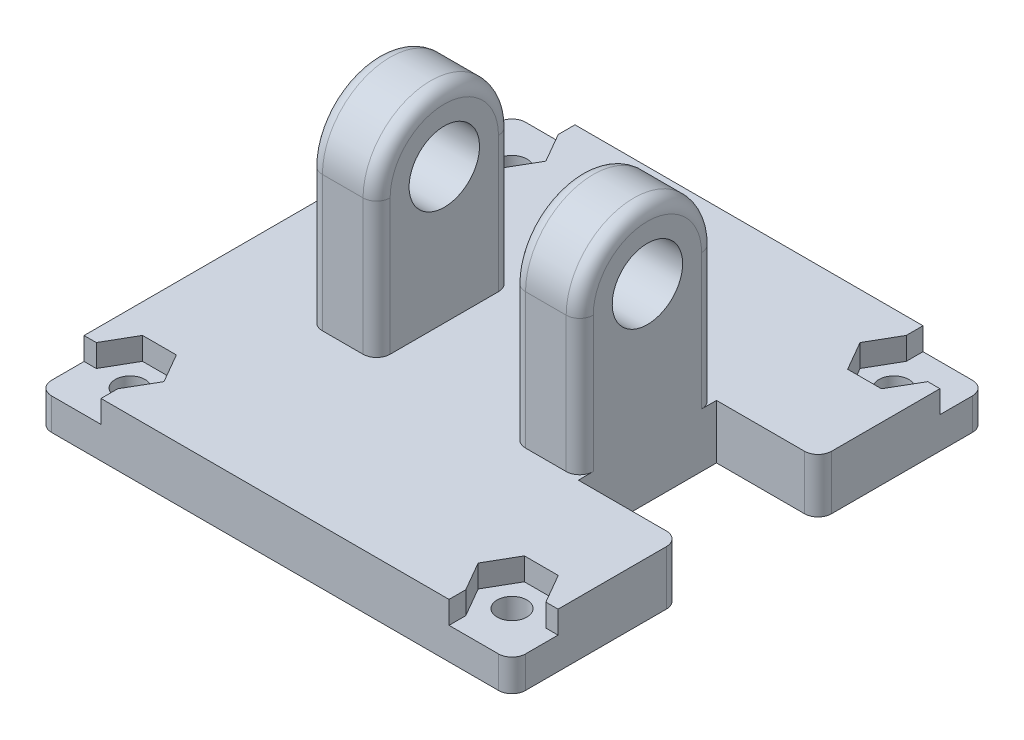
SolidWorks part; units mm, degrees
ref_plane "Plan de face" through (0, 0, 0) normal (0, 0, 1) x (1, 0, 0)
ref_plane "Plan de dessus" through (0, 0, 0) normal (0, 1, 0) x (1, 0, 0)
ref_plane "Plan de droite" through (0, 0, 0) normal (1, 0, 0) x (0, 0, -1)
sketch "Esquisse2" plane through (0, 0, 0) normal (1, 0, 0) x (0, 0, -1)
  line L0 (5, 0) -> (5, -10)
  line L2 (-5, 0) -> (-5, -10)
  line L3 (-5, -10) -> (5, -10)
  circle A0 centre (0, 0) radius 2.6
  arc A2 (5, 0) -> (-5, 0) centre (0, 0) ccw
  dimension "D1" = 5.2
  dimension "D2" = 10
  dimension "D3" = 5
  dimension "D4" = 5
extrude "Boss.-Extru.1" add sketch "Esquisse2" along normal mid plane 20
sketch "Esquisse4" plane through (0, -10, 0) normal (0, -1, 0) x (1, 0, 0)
  line L1 (-17.5, -17.5) -> (17.5, -17.5)
  line L2 (-17.5, -17.5) -> (-17.5, 17.5)
  line L3 (-17.5, 17.5) -> (17.5, 17.5)
  line L4 (17.5, -17.5) -> (17.5, 17.5)
  dimension "D1" = 35
  dimension "D2" = 35
  dimension "D3" = 17.5
  dimension "D4" = 17.5
extrude "Boss.-Extru.2" add sketch "Esquisse4" along normal blind 4
sketch "Esquisse5" plane through (0, -10, 0) normal (0, 1, 0) x (1, 0, 0)
  circle A0 centre (14.1, -14.1) radius 1.1
  circle A1 centre (14.1, 14.1) radius 1.1
  circle A2 centre (-14.1, 14.1) radius 1.1
  circle A3 centre (-14.1, -14.1) radius 1.1
  point P15 (0, 0)
  dimension "D1" = 2.2
  dimension "D2" = 28.2
  dimension "D3" = 28.2
  dimension "D4" = 14.1
  dimension "D5" = 14.1
extrude "Enlèv. mat.-Extru.1" cut sketch "Esquisse5" against normal up to next contours A0
sketch "Esquisse6" plane through (0, 0, 5) normal (0, 0, 1) x (1, 0, 0)
  line L0 (10, -10) -> (-10, -10) construction
  line L1 (-5, 6.1864) -> (5, 6.1864)
  line L2 (-5, 6.1864) -> (-5, -10)
  line L3 (-5, -10) -> (5, -10)
  line L4 (5, 6.1864) -> (5, -10)
  dimension "D1" = 5
  dimension "D2" = 10
extrude "Enlèv. mat.-Extru.2" cut sketch "Esquisse6" against normal through all
sketch "Esquisse7" plane through (0, -10, 0) normal (0, 1, 0) x (1, 0, 0)
  line L8 (-11.6, -14.1) -> (-12.85, -11.9349)
  line L9 (-12.85, -11.9349) -> (-15.35, -11.9349)
  line L10 (-15.35, -11.9349) -> (-16.6, -14.1)
  line L11 (-16.6, -14.1) -> (-15.35, -16.2651)
  line L12 (-15.35, -16.2651) -> (-12.85, -16.2651)
  line L13 (-12.85, -16.2651) -> (-11.6, -14.1)
  line L14 (16.6, -14.1) -> (15.35, -11.9349)
  line L15 (15.35, -11.9349) -> (12.85, -11.9349)
  line L16 (12.85, -11.9349) -> (11.6, -14.1)
  line L17 (11.6, -14.1) -> (12.85, -16.2651)
  line L18 (12.85, -16.2651) -> (15.35, -16.2651)
  line L19 (15.35, -16.2651) -> (16.6, -14.1)
  line L20 (16.6, 14.1) -> (15.35, 16.2651)
  line L21 (15.35, 16.2651) -> (12.85, 16.2651)
  line L22 (12.85, 16.2651) -> (11.6, 14.1)
  line L23 (11.6, 14.1) -> (12.85, 11.9349)
  line L24 (12.85, 11.9349) -> (15.35, 11.9349)
  line L25 (15.35, 11.9349) -> (16.6, 14.1)
  line L26 (-11.6, 14.1) -> (-12.85, 16.2651)
  line L27 (-12.85, 16.2651) -> (-15.35, 16.2651)
  line L28 (-15.35, 16.2651) -> (-16.6, 14.1)
  line L29 (-16.6, 14.1) -> (-15.35, 11.9349)
  line L30 (-15.35, 11.9349) -> (-12.85, 11.9349)
  line L31 (-12.85, 11.9349) -> (-11.6, 14.1)
  line L32 (-17.5, 17.5) -> (17.5, 17.5) construction
  line L33 (17.5, -17.5) -> (-17.5, -17.5) construction
  circle A5 centre (-14.1, -14.1) radius 2.1651 construction
  circle A6 centre (14.1, -14.1) radius 2.1651 construction
  circle A7 centre (14.1, 14.1) radius 2.1651 construction
  circle A8 centre (-14.1, 14.1) radius 2.1651 construction
  dimension "D1" = 2.5
  dimension "D2" = 2.5
  dimension "D3" = 2.5
  dimension "D4" = 2.5
extrude "Enlèv. mat.-Extru.3" cut sketch "Esquisse7" against normal blind 1.66
sketch "Esquisse8" plane through (0, -10, 0) normal (0, 1, 0) x (1, 0, 0)
  line L10 (17.5, 17.5) -> (17.5, -17.5) construction
  line L11 (17.5, 5.1) -> (10, 5.1)
  line L12 (17.5, 5.1) -> (17.5, -5.1)
  line L13 (17.5, -5.1) -> (10, -5.1)
  line L14 (10, 5.1) -> (10, -5.1)
  line L15 (10, -5) -> (10, 5) construction
  point P2 (0, 0)
  dimension "D1" = 10.2
  dimension "D2" = 5.1
extrude "Enlèv. mat.-Extru.4" cut sketch "Esquisse8" against normal up to next
fillet "Congé1" radius 1 18 edges at (5, -5, -5) (5, -5, 5) (-5, -5, 5) (-5, -5, -5) (10, -5, -5) (10, -5, 5) (-10, -5, -5) (-10, -5, 5) (5, 5, 0) (-5, 5, 0) (10, 5, 0) (-10, 5, 0) (-17.5, -12, -17.5) (-17.5, -12, 17.5) (17.5, -12, -17.5) (17.5, -12, 17.5) (17.5, -12, 5.1) (17.5, -12, -5.1)
sketch "Esquisse9" plane through (0, -10, 0) normal (0, 1, 0) x (1, 0, 0)
  line L0 (-12.85, 16.2651) -> (-12.85, 18.6987)
  line L1 (-12.85, 18.6987) -> (-21.4953, 18.6987)
  line L2 (-21.4953, 18.6987) -> (-21.4953, 14.1)
  line L3 (-21.4953, 14.1) -> (-16.6, 14.1)
  line L4 (-16.6, 14.1) -> (-12.85, 16.2651)
  line L5 (12.85, 16.2651) -> (16.6, 14.1)
  line L6 (16.6, 14.1) -> (20.9602, 14.1)
  line L7 (20.9602, 14.1) -> (20.9602, 18.6997)
  line L8 (20.9602, 18.6997) -> (12.85, 18.6997)
  line L9 (12.85, 18.6997) -> (12.85, 16.2651)
  line L10 (16.6, -14.1) -> (12.85, -16.2651)
  line L11 (12.85, -16.2651) -> (12.85, -19.9614)
  line L12 (12.85, -19.9614) -> (19.4885, -19.9614)
  line L13 (19.4885, -19.9614) -> (19.4885, -14.1)
  line L14 (19.4885, -14.1) -> (16.6, -14.1)
  line L15 (-12.85, -16.2651) -> (-16.6, -14.1)
  line L16 (-16.6, -14.1) -> (-22.3796, -14.1)
  line L17 (-22.3796, -14.1) -> (-22.3796, -21.0355)
  line L18 (-22.3796, -21.0355) -> (-12.85, -21.0355)
  line L19 (-12.85, -21.0355) -> (-12.85, -16.2651)
extrude "Enlèv. mat.-Extru.5" cut sketch "Esquisse9" against normal up to surface (1.66 mm away) up to face at (-14.1, -11.66, 14.1)
